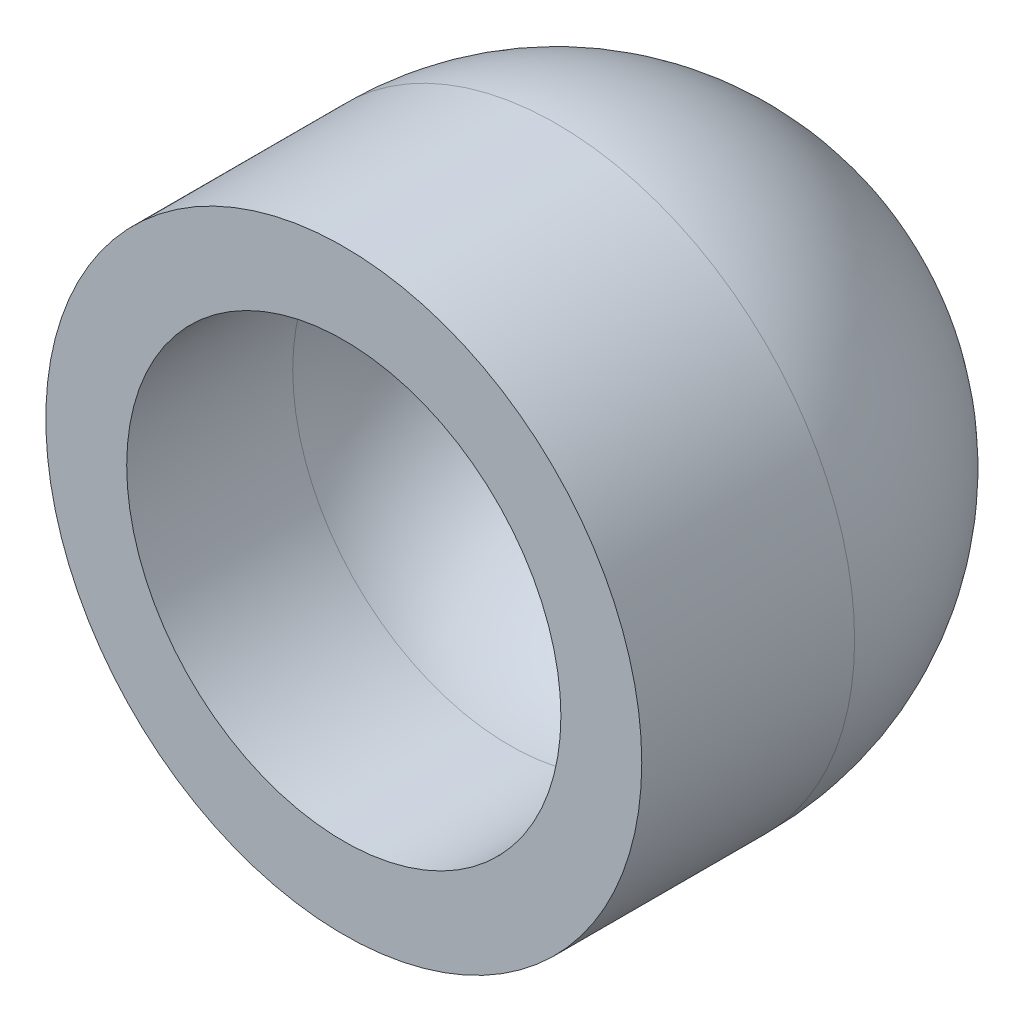
SolidWorks part; units mm, degrees
ref_plane "Front Plane" through (0, 0, 0) normal (0, 0, 1) x (1, 0, 0)
ref_plane "Top Plane" through (0, 0, 0) normal (0, 1, 0) x (1, 0, 0)
ref_plane "Right Plane" through (0, 0, 0) normal (1, 0, 0) x (0, 0, -1)
sketch "Sketch1" plane through (0, 0, 0) normal (0, 1, 0) x (1, 0, 0)
  line L0 (0, 0) -> (0, 3.81)
  line L1 (6.477, -6.477) -> (6.477, -11.43)
  line L2 (6.477, -11.43) -> (8.89, -11.43)
  line L3 (8.89, -11.43) -> (8.89, -5.08)
  arc A0 (0, 0) -> (6.477, -6.477) centre (0, -6.477) cw
  arc A1 (0, 3.81) -> (8.89, -5.08) centre (0, -5.08) cw
  dimension "D1" = 6.477
  dimension "D2" = 15.24
  dimension "D3" = 8.89
  dimension "D4" = 3.81
revolve "Revolve1" add sketch "Sketch1" angle 360 about L0
